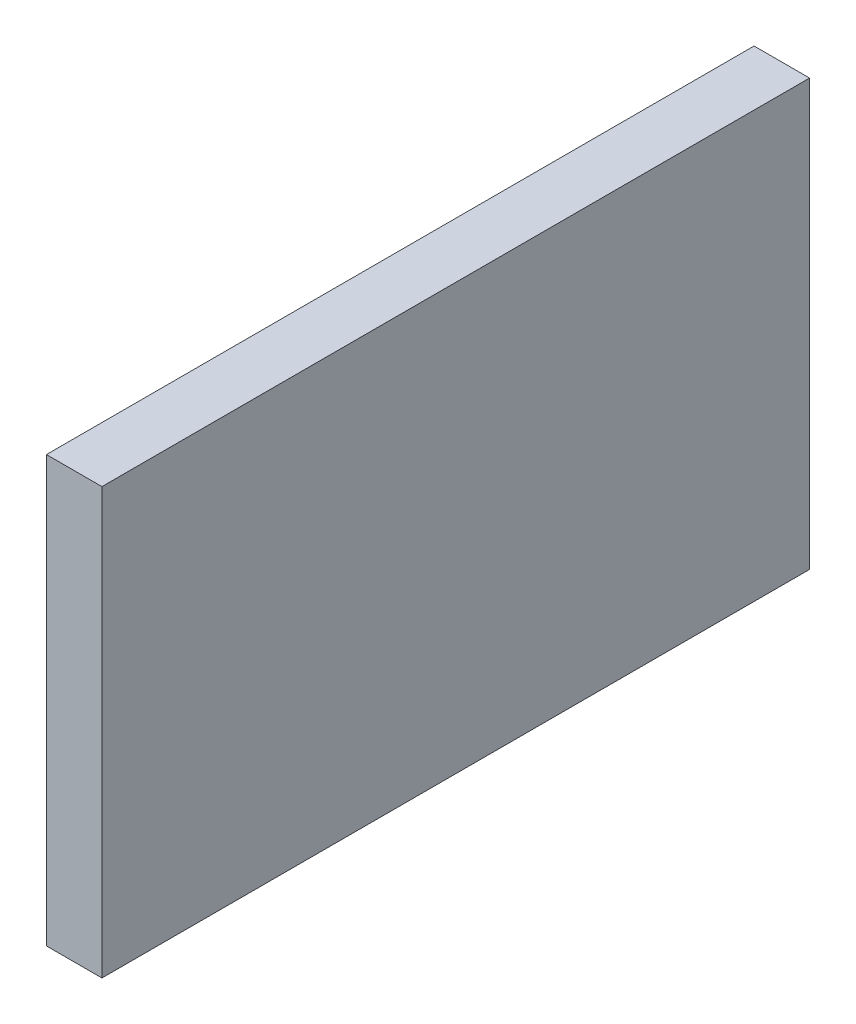
SolidWorks part; units mm, degrees
material "Acrylic (Medium-high impact)"
ref_plane "Front Plane" through (0, 0, 0) normal (0, 0, 1) x (1, 0, 0)
ref_plane "Top Plane" through (0, 0, 0) normal (0, 1, 0) x (1, 0, 0)
ref_plane "Right Plane" through (0, 0, 0) normal (1, 0, 0) x (0, 0, -1)
sketch "Sketch1" plane through (0, 0, 37.7805) normal (0, 0, 1) x (1, 0, 0)
  line L0 (13.9215, 21.8233) -> (8.9215, 21.8233) construction
  line L1 (8.3577, 44.8268) -> (11.3577, 44.8268)
  line L2 (8.3577, 44.8268) -> (8.3577, 21.8233)
  line L3 (8.3577, 21.8233) -> (11.3577, 21.8233)
  line L4 (11.3577, 44.8268) -> (11.3577, 21.8233)
  dimension "D1" = 3
extrude "Boss-Extrude1" add sketch "Sketch1" along normal up to surface (38.25 mm away)
